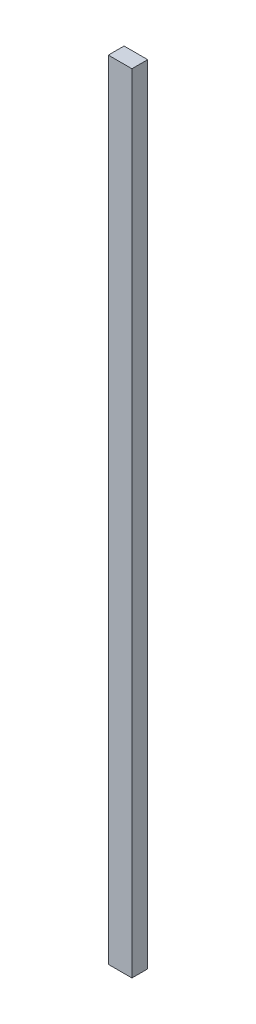
SolidWorks part; units mm, degrees
ref_plane "Front Plane" through (0, 0, 0) normal (0, 0, 1) x (1, 0, 0)
ref_plane "Top Plane" through (0, 0, 0) normal (0, 1, 0) x (1, 0, 0)
ref_plane "Right Plane" through (0, 0, 0) normal (1, 0, 0) x (0, 0, -1)
sketch "Sketch1" plane through (0, 0, 0) normal (0, 1, 0) x (1, 0, 0)
  line L1 (-6, -4) -> (6, -4)
  line L2 (-6, -4) -> (-6, 4)
  line L3 (-6, 4) -> (6, 4)
  line L4 (6, -4) -> (6, 4)
  line L5 (-6, -4) -> (6, 4) construction
  line L6 (-6, 4) -> (6, -4) construction
  point P0 (0, 0)
  dimension "D1" = 12
  dimension "D2" = 8
extrude "Boss-Extrude1" add sketch "Sketch1" along normal blind 400
